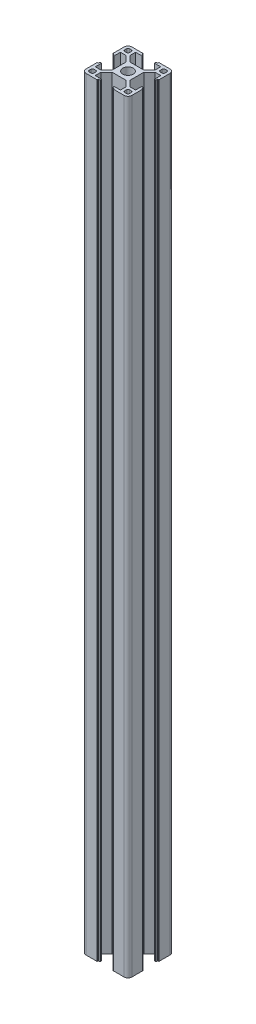
SolidWorks part; units mm, degrees
material "6063-T5"
ref_plane "前视基准面" through (0, 0, 0) normal (0, 0, 1) x (1, 0, 0)
ref_plane "上视基准面" through (0, 0, 0) normal (0, 1, 0) x (1, 0, 0)
ref_plane "右视基准面" through (0, 0, 0) normal (1, 0, 0) x (0, 0, -1)
sketch "草图3" plane through (0, 0, 0) normal (0, 1, 0) x (1, 0, 0)
  line L0 (0, 0) -> (-15, -15) construction
  line L1 (-15, -15) -> (-15, 0) construction
  line L2 (-15, 0) -> (0, 0) construction
  line L3 (-15, -12.5) -> (-15, -5.4)
  line L4 (-14.8, -5.2) -> (-14.4, -5.2)
  line L5 (-14.2, -5) -> (-14.2, -4.3)
  line L6 (-14, -4.1) -> (-13.2, -4.1)
  line L7 (-13.2, -4.1) -> (-13.2, -8.25)
  line L8 (-13.2, -8.25) -> (-9.5228, -8.25)
  line L9 (-9.5228, -8.25) -> (-5.8, -4.5272)
  line L10 (-5.8, -4.5272) -> (-5.8, 4.5272)
  line L11 (-13.2, -12.2) -> (-13.2, -11.05)
  line L12 (-12.2, -10.05) -> (-11.05, -10.05)
  line L13 (-4.5272, -5.8) -> (4.5272, -5.8)
  line L14 (-8.25, -9.5228) -> (-4.5272, -5.8)
  line L15 (-12.2, -13.2) -> (-11.05, -13.2)
  line L16 (-10.05, -12.2) -> (-10.05, -11.05)
  line L17 (-5.2, -14.8) -> (-5.2, -14.4)
  line L18 (-5, -14.2) -> (-4.3, -14.2)
  line L19 (-4.1, -14) -> (-4.1, -13.2)
  line L20 (-4.1, -13.2) -> (-8.25, -13.2)
  line L21 (-8.25, -13.2) -> (-8.25, -9.5228)
  line L22 (-12.5, -15) -> (-5.4, -15)
  line L23 (-12.5, 15) -> (-5.4, 15)
  line L24 (-8.25, 13.2) -> (-8.25, 9.5228)
  line L25 (-4.1, 13.2) -> (-8.25, 13.2)
  line L26 (-4.1, 14) -> (-4.1, 13.2)
  line L27 (-5, 14.2) -> (-4.3, 14.2)
  line L28 (-5.2, 14.8) -> (-5.2, 14.4)
  line L29 (-10.05, 12.2) -> (-10.05, 11.05)
  line L30 (-12.2, 13.2) -> (-11.05, 13.2)
  line L31 (-8.25, 9.5228) -> (-4.5272, 5.8)
  line L32 (-4.5272, 5.8) -> (4.5272, 5.8)
  line L33 (-12.2, 10.05) -> (-11.05, 10.05)
  line L34 (-13.2, 12.2) -> (-13.2, 11.05)
  line L35 (-9.5228, 8.25) -> (-5.8, 4.5272)
  line L36 (-13.2, 8.25) -> (-9.5228, 8.25)
  line L37 (-13.2, 4.1) -> (-13.2, 8.25)
  line L38 (-14, 4.1) -> (-13.2, 4.1)
  line L39 (-14.2, 5) -> (-14.2, 4.3)
  line L40 (-14.8, 5.2) -> (-14.4, 5.2)
  line L41 (-15, 12.5) -> (-15, 5.4)
  line L42 (0, 0) -> (0, -12.3268) construction
  line L43 (15, 12.5) -> (15, 5.4)
  line L44 (14.8, 5.2) -> (14.4, 5.2)
  line L45 (14.2, 5) -> (14.2, 4.3)
  line L46 (14, 4.1) -> (13.2, 4.1)
  line L47 (13.2, 4.1) -> (13.2, 8.25)
  line L48 (13.2, 8.25) -> (9.5228, 8.25)
  line L49 (9.5228, 8.25) -> (5.8, 4.5272)
  line L50 (13.2, 12.2) -> (13.2, 11.05)
  line L51 (12.2, 10.05) -> (11.05, 10.05)
  line L52 (8.25, 9.5228) -> (4.5272, 5.8)
  line L53 (12.2, 13.2) -> (11.05, 13.2)
  line L54 (10.05, 12.2) -> (10.05, 11.05)
  line L55 (5.2, 14.8) -> (5.2, 14.4)
  line L56 (5, 14.2) -> (4.3, 14.2)
  line L57 (4.1, 14) -> (4.1, 13.2)
  line L58 (4.1, 13.2) -> (8.25, 13.2)
  line L59 (8.25, 13.2) -> (8.25, 9.5228)
  line L60 (12.5, 15) -> (5.4, 15)
  line L61 (12.5, -15) -> (5.4, -15)
  line L62 (8.25, -13.2) -> (8.25, -9.5228)
  line L63 (4.1, -13.2) -> (8.25, -13.2)
  line L64 (4.1, -14) -> (4.1, -13.2)
  line L65 (5, -14.2) -> (4.3, -14.2)
  line L66 (5.2, -14.8) -> (5.2, -14.4)
  line L67 (10.05, -12.2) -> (10.05, -11.05)
  line L68 (12.2, -13.2) -> (11.05, -13.2)
  line L69 (8.25, -9.5228) -> (4.5272, -5.8)
  line L70 (12.2, -10.05) -> (11.05, -10.05)
  line L71 (13.2, -12.2) -> (13.2, -11.05)
  line L72 (5.8, -4.5272) -> (5.8, 4.5272)
  line L73 (9.5228, -8.25) -> (5.8, -4.5272)
  line L74 (13.2, -8.25) -> (9.5228, -8.25)
  line L75 (13.2, -4.1) -> (13.2, -8.25)
  line L76 (14, -4.1) -> (13.2, -4.1)
  line L77 (14.2, -5) -> (14.2, -4.3)
  line L78 (14.8, -5.2) -> (14.4, -5.2)
  line L79 (15, -12.5) -> (15, -5.4)
  circle A0 centre (0, 0) radius 3.4
  arc A1 (-12.5, 15) -> (-15, 12.5) centre (-12.5, 12.5) ccw
  arc A2 (15, 12.5) -> (12.5, 15) centre (12.5, 12.5) ccw
  arc A3 (12.5, -15) -> (15, -12.5) centre (12.5, -12.5) ccw
  arc A4 (-15, -12.5) -> (-12.5, -15) centre (-12.5, -12.5) ccw
  arc A5 (-12.2, 13.2) -> (-13.2, 12.2) centre (-12.2, 12.2) ccw
  arc A6 (-12.2, 10.05) -> (-13.2, 11.05) centre (-12.2, 11.05) cw
  arc A7 (-10.05, 11.05) -> (-11.05, 10.05) centre (-11.05, 11.05) cw
  arc A8 (-10.05, 12.2) -> (-11.05, 13.2) centre (-11.05, 12.2) ccw
  arc A9 (11.05, 10.05) -> (10.05, 11.05) centre (11.05, 11.05) cw
  arc A10 (11.05, 13.2) -> (10.05, 12.2) centre (11.05, 12.2) ccw
  arc A11 (13.2, 12.2) -> (12.2, 13.2) centre (12.2, 12.2) ccw
  arc A12 (13.2, 11.05) -> (12.2, 10.05) centre (12.2, 11.05) cw
  arc A13 (12.2, -10.05) -> (13.2, -11.05) centre (12.2, -11.05) cw
  arc A14 (10.05, -11.05) -> (11.05, -10.05) centre (11.05, -11.05) cw
  arc A15 (10.05, -12.2) -> (11.05, -13.2) centre (11.05, -12.2) ccw
  arc A16 (12.2, -13.2) -> (13.2, -12.2) centre (12.2, -12.2) ccw
  arc A17 (-13.2, -11.05) -> (-12.2, -10.05) centre (-12.2, -11.05) cw
  arc A18 (-11.05, -10.05) -> (-10.05, -11.05) centre (-11.05, -11.05) cw
  arc A19 (-11.05, -13.2) -> (-10.05, -12.2) centre (-11.05, -12.2) ccw
  arc A20 (-13.2, -12.2) -> (-12.2, -13.2) centre (-12.2, -12.2) ccw
  arc A21 (-15, -5.4) -> (-14.8, -5.2) centre (-14.8, -5.4) cw
  arc A22 (-14.4, -5.2) -> (-14.2, -5) centre (-14.4, -5) ccw
  arc A23 (-14.2, -4.3) -> (-14, -4.1) centre (-14, -4.3) cw
  arc A24 (-14, 4.1) -> (-14.2, 4.3) centre (-14, 4.3) cw
  arc A25 (-14.2, 5) -> (-14.4, 5.2) centre (-14.4, 5) ccw
  arc A26 (-14.8, 5.2) -> (-15, 5.4) centre (-14.8, 5.4) cw
  arc A27 (-5.4, 15) -> (-5.2, 14.8) centre (-5.4, 14.8) cw
  arc A28 (-5, 14.2) -> (-5.2, 14.4) centre (-5, 14.4) cw
  arc A29 (-4.1, 14) -> (-4.3, 14.2) centre (-4.3, 14) ccw
  arc A30 (5.2, 14.8) -> (5.4, 15) centre (5.4, 14.8) cw
  arc A31 (5.2, 14.4) -> (5, 14.2) centre (5, 14.4) cw
  arc A32 (4.3, 14.2) -> (4.1, 14) centre (4.3, 14) ccw
  arc A33 (15, 5.4) -> (14.8, 5.2) centre (14.8, 5.4) cw
  arc A34 (14.4, 5.2) -> (14.2, 5) centre (14.4, 5) ccw
  arc A35 (14.2, 4.3) -> (14, 4.1) centre (14, 4.3) cw
  arc A36 (14, -4.1) -> (14.2, -4.3) centre (14, -4.3) cw
  arc A37 (14.2, -5) -> (14.4, -5.2) centre (14.4, -5) ccw
  arc A38 (14.8, -5.2) -> (15, -5.4) centre (14.8, -5.4) cw
  arc A39 (5.4, -15) -> (5.2, -14.8) centre (5.4, -14.8) cw
  arc A40 (5, -14.2) -> (5.2, -14.4) centre (5, -14.4) cw
  arc A41 (4.1, -14) -> (4.3, -14.2) centre (4.3, -14) ccw
  arc A42 (-5.2, -14.4) -> (-5, -14.2) centre (-5, -14.4) cw
  arc A43 (-4.3, -14.2) -> (-4.1, -14) centre (-4.3, -14) ccw
  arc A44 (-5.2, -14.8) -> (-5.4, -15) centre (-5.4, -14.8) cw
  point P38 (-5.8, 0)
  point P46 (0, 5.8)
  point P47 (0, -5.8)
  point P83 (5.8, 0)
  point P87 (-15, 15)
  point P90 (15, 15)
  point P93 (15, -15)
  point P99 (-13.2, 13.2)
  point P102 (-13.2, 10.05)
  point P105 (-10.05, 10.05)
  point P108 (-10.05, 13.2)
  point P111 (10.05, 10.05)
  point P114 (10.05, 13.2)
  point P117 (13.2, 13.2)
  point P120 (13.2, 10.05)
  point P123 (13.2, -10.05)
  point P126 (10.05, -10.05)
  point P129 (10.05, -13.2)
  point P132 (13.2, -13.2)
  point P135 (-13.2, -10.05)
  point P138 (-10.05, -10.05)
  point P141 (-10.05, -13.2)
  point P144 (-13.2, -13.2)
  point P147 (-15, -5.2)
  point P150 (-14.2, -5.2)
  point P153 (-14.2, -4.1)
  point P156 (-14.2, 4.1)
  point P159 (-14.2, 5.2)
  point P162 (-15, 5.2)
  point P165 (-5.2, 15)
  point P168 (-5.2, 14.2)
  point P171 (-4.1, 14.2)
  point P174 (5.2, 15)
  point P177 (5.2, 14.2)
  point P180 (4.1, 14.2)
  point P183 (15, 5.2)
  point P186 (14.2, 5.2)
  point P189 (14.2, 4.1)
  point P192 (14.2, -4.1)
  point P195 (14.2, -5.2)
  point P198 (15, -5.2)
  point P201 (5.2, -15)
  point P204 (5.2, -14.2)
  point P207 (4.1, -14.2)
  point P210 (-5.2, -14.2)
  point P213 (-4.1, -14.2)
  point P216 (-5.2, -15)
  dimension "D11" = 6.8
  dimension "D12" = 2.5
  dimension "D13" = 1
  dimension "D14" = 0.2
  dimension "D2" = 15
  dimension "D3" = 4.1
  dimension "D4" = 5.2
  dimension "D5" = 0.8
  dimension "D6" = 1.8
  dimension "D7" = 9.2
  dimension "D8" = 8.25
  dimension "D9" = 0.9
  dimension "D10" = 1.8
extrude "凸台-拉伸1" add sketch "草图3" along normal blind 500
ref_plane "基准面1" through (-10.05, 250, 12.2) normal (0, -1, 0) x (-1, 0, 0)
